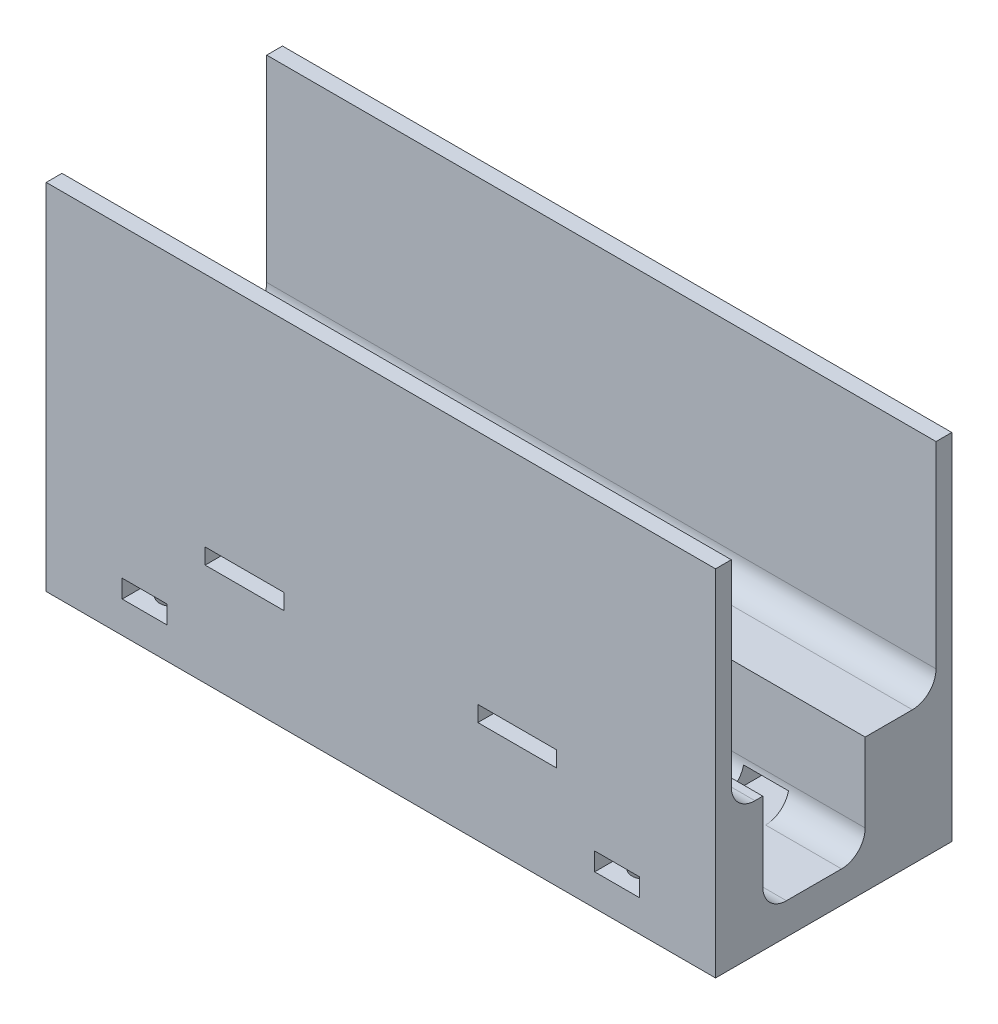
SolidWorks part; units mm, degrees
ref_plane "前视基准面" through (0, 0, 0) normal (0, 0, 1) x (1, 0, 0)
ref_plane "上视基准面" through (0, 0, 0) normal (0, 1, 0) x (1, 0, 0)
ref_plane "右视基准面" through (0, 0, 0) normal (1, 0, 0) x (0, 0, -1)
sketch "草图1" plane through (0, 0, 0) normal (0, 1, 0) x (1, 0, 0)
  line L1 (-42.5, 15) -> (42.5, 15)
  line L2 (-42.5, 15) -> (-42.5, -15)
  line L3 (-42.5, -15) -> (42.5, -15)
  line L4 (42.5, 15) -> (42.5, -15)
  line L5 (-42.5, 15) -> (42.5, -15) construction
  line L6 (-42.5, -15) -> (42.5, 15) construction
  point P0 (0, 0)
  dimension "D1" = 30
  dimension "D2" = 85
extrude "凸台-拉伸1" add sketch "草图1" along normal blind 45
sketch "草图2" plane through (0, 45, 0) normal (0, 1, 0) x (1, 0, 0)
  line L0 (42.5, -15) -> (42.5, 15) construction
  line L1 (-42.5, 13) -> (42.5, 13)
  line L2 (-42.5, 13) -> (-42.5, -13)
  line L3 (-42.5, -13) -> (42.5, -13)
  line L4 (42.5, 13) -> (42.5, -13)
  line L5 (-42.5, 13) -> (42.5, -13) construction
  line L6 (-42.5, -13) -> (42.5, 13) construction
  point P0 (0, 0)
  dimension "D1" = 26
extrude "切除-拉伸1" cut sketch "草图2" against normal blind 28
sketch "草图3" plane through (0, 17, 0) normal (0, 1, 0) x (1, 0, 0)
  line L0 (-42.5, 13) -> (-42.5, -13) construction
  line L1 (-42.5, -9) -> (42.5, -9)
  line L2 (-42.5, -9) -> (-42.5, 4)
  line L3 (-42.5, 4) -> (42.5, 4)
  line L4 (42.5, -9) -> (42.5, 4)
  line L5 (42.5, -13) -> (42.5, 13) construction
  line L6 (-42.5, -13) -> (42.5, -13) construction
  dimension "D1" = 13
  dimension "D2" = 4
extrude "切除-拉伸3" cut sketch "草图3" against normal blind 13
sketch "草图4" plane through (0, 0, 15) normal (0, 0, 1) x (1, 0, 0)
  line L0 (0, 0) -> (0, 49.9229) construction
  line L1 (-22.3157, 15) -> (-12.3157, 15)
  line L2 (-22.3157, 15) -> (-22.3157, 13)
  line L3 (-22.3157, 13) -> (-12.3157, 13)
  line L4 (-12.3157, 15) -> (-12.3157, 13)
  line L5 (-22.3157, 15) -> (-12.3157, 13) construction
  line L6 (-22.3157, 13) -> (-12.3157, 15) construction
  line L7 (22.3157, 13) -> (12.3157, 13)
  line L8 (12.3157, 15) -> (12.3157, 13)
  line L9 (22.3157, 15) -> (12.3157, 15)
  line L10 (22.3157, 15) -> (22.3157, 13)
  line L11 (-42.5, 0) -> (42.5, 0) construction
  point P0 (-17.3157, 14)
  dimension "D1" = 2
  dimension "D2" = 10
  dimension "D3" = 13
extrude "切除-拉伸4" cut sketch "草图4" against normal through all
fillet "圆角1" radius 3 4 edges at (0, 17, -13) (0, 17, 13) (0, 4, 9) (0, 4, -4)
sketch "草图5" plane through (0, 0, 0) normal (0, -1, 0) x (1, 0, 0)
  line L0 (-30, 11.5) -> (-30, -11.5) construction
  line L1 (0, 0) -> (0, 27.553) construction
  line L2 (0, 0) -> (-30, 0) construction
  circle A0 centre (-30, 11.5) radius 1.6
  circle A1 centre (-30, -11.5) radius 1.6
  circle A2 centre (30, -11.5) radius 1.6
  circle A3 centre (30, 11.5) radius 1.6
  dimension "D1" = 3.2
  dimension "D2" = 3.2
  dimension "D3" = 60
  dimension "D4" = 23
extrude "切除-拉伸5" cut sketch "草图5" against normal blind 8
sketch "草图6" plane through (0, 0, 15) normal (0, 0, 1) x (1, 0, 0)
  line L0 (-42.5, 0) -> (42.5, 0) construction
  line L1 (-32.85, 6.3) -> (-27.15, 6.3)
  line L2 (-32.85, 6.3) -> (-32.85, 4)
  line L3 (-32.85, 4) -> (-27.15, 4)
  line L4 (-27.15, 6.3) -> (-27.15, 4)
  line L5 (-32.85, 6.3) -> (-27.15, 4) construction
  line L6 (-32.85, 4) -> (-27.15, 6.3) construction
  line L7 (0, 0) -> (0, 49.1399) construction
  line L8 (32.85, 4) -> (27.15, 4)
  line L9 (27.15, 6.3) -> (27.15, 4)
  line L10 (32.85, 6.3) -> (27.15, 6.3)
  line L11 (32.85, 6.3) -> (32.85, 4)
  point P0 (-30, 5.15)
  dimension "D1" = 5.7
  dimension "D2" = 2.3
  dimension "D3" = 4
  dimension "D4" = 30
extrude "切除-拉伸6" cut sketch "草图6" against normal through all
